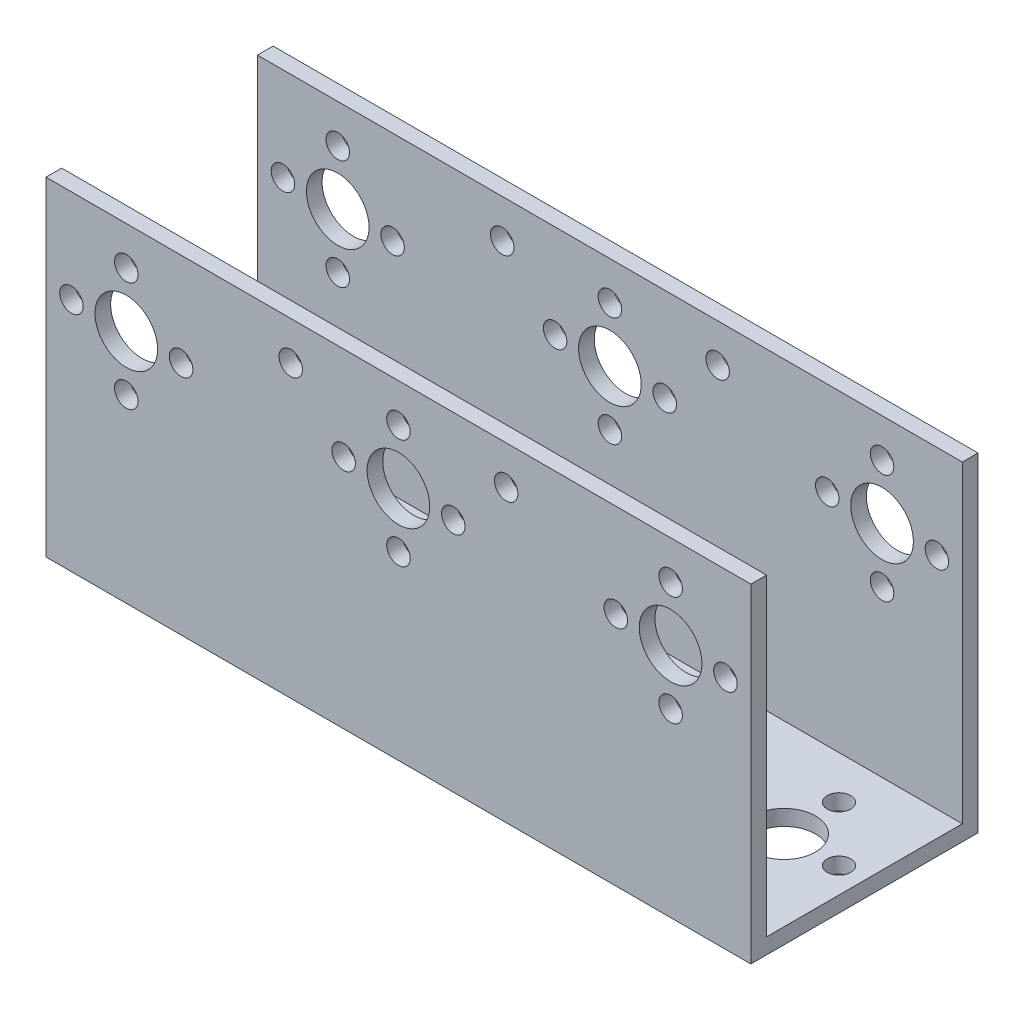
SolidWorks part; units mm, degrees
material "5052-H32"
ref_plane "Front Plane" through (0, 0, 0) normal (0, 0, 1) x (1, 0, 0)
ref_plane "Top Plane" through (0, 0, 0) normal (0, 1, 0) x (1, 0, 0)
ref_plane "Right Plane" through (0, 0, 0) normal (1, 0, 0) x (0, 0, -1)
sketch "Sketch1" plane through (0, 0, 0) normal (0, 1, 0) x (1, 0, 0)
  line L1 (45, -12.5) -> (-45, -12.5)
  line L2 (45, -12.5) -> (45, 12.5)
  line L3 (45, 12.5) -> (-45, 12.5)
  line L4 (-45, -12.5) -> (-45, 12.5)
  line L5 (45, -12.5) -> (-45, 12.5) construction
  line L6 (45, 12.5) -> (-45, -12.5) construction
  circle A0 centre (0, 0) radius 4
  circle A1 centre (34.75, 0) radius 4
  circle A2 centre (0, 7) radius 1.5
  circle A3 centre (7, 0) radius 1.5
  circle A4 centre (-7, 0) radius 1.5
  circle A5 centre (0, -7) radius 1.5
  circle A6 centre (-34.75, 0) radius 4
  circle A7 centre (34.75, 7) radius 1.5
  circle A8 centre (41.75, 0) radius 1.5
  circle A9 centre (34.75, -7) radius 1.5
  circle A10 centre (27.75, 0) radius 1.5
  circle A12 centre (-34.75, 7) radius 1.5
  circle A13 centre (-27.75, 0) radius 1.5
  circle A14 centre (-34.75, -7) radius 1.5
  circle A15 centre (-41.75, 0) radius 1.5
  point P0 (0, 0)
  dimension "D3" = 3
  dimension "D4" = 3
  dimension "D5" = 3
  dimension "D6" = 3
  dimension "D7" = 3
  dimension "D8" = 8
  dimension "D9" = 3
  dimension "D10" = 3
  dimension "D11" = 3
  dimension "D12" = 34.75
  dimension "D13" = 8
  dimension "D15" = 3
  dimension "D16" = 3
  dimension "D17" = 3
  dimension "D18" = 3
  dimension "D20" = 8
  dimension "D1" = 25
  dimension "D2" = 90
  dimension "D14" = 34.75
extrude "Boss-Extrude1" add sketch "Sketch1" along normal blind 2
sketch "Sketch2" plane through (0, 0, 12.5) normal (0, 0, 1) x (1, 0, 0)
  line L1 (-45, 0) -> (45, 0)
  line L2 (-45, 0) -> (-45, 42)
  line L3 (-45, 42) -> (45, 42)
  line L4 (45, 0) -> (45, 42)
  circle A0 centre (0, 30.08) radius 4
  circle A2 centre (0, 37.08) radius 1.5
  circle A3 centre (7, 30.08) radius 1.5
  circle A4 centre (0, 23.08) radius 1.5
  circle A5 centre (-7, 30.08) radius 1.5
  circle A7 centre (34.75, 30.08) radius 4
  circle A8 centre (34.75, 37.08) radius 1.5
  circle A9 centre (41.75, 30.08) radius 1.5
  circle A10 centre (34.75, 23.08) radius 1.5
  circle A11 centre (27.75, 30.08) radius 1.5
  circle A12 centre (-34.75, 30.08) radius 4
  circle A14 centre (-34.75, 37.08) radius 1.5
  circle A15 centre (-27.75, 30.08) radius 1.5
  circle A16 centre (-34.75, 23.08) radius 1.5
  circle A17 centre (-41.75, 30.08) radius 1.5
  circle A18 centre (13.75, 37.08) radius 1.5
  circle A19 centre (-13.75, 37.08) radius 1.5
  dimension "D5" = 8
  dimension "D6" = 3
  dimension "D7" = 3
  dimension "D8" = 3
  dimension "D9" = 3
  dimension "D11" = 8
  dimension "D12" = 3
  dimension "D13" = 3
  dimension "D14" = 3
  dimension "D15" = 3
  dimension "D17" = 8
  dimension "D18" = 3
  dimension "D19" = 3
  dimension "D20" = 3
  dimension "D21" = 3
  dimension "D24" = 3
  dimension "D25" = 3
  dimension "D1" = 42
  dimension "D2" = 90
  dimension "D3" = 30.08
  dimension "D22" = 34.75
  dimension "D23" = 34.75
  dimension "D26" = 13.75
  dimension "D27" = 13.75
extrude "Boss-Extrude2" add sketch "Sketch2" along normal blind 2
mirror "Mirror1" about plane through (0, 0, 0) normal (0, 0, 1) of bodies 102
